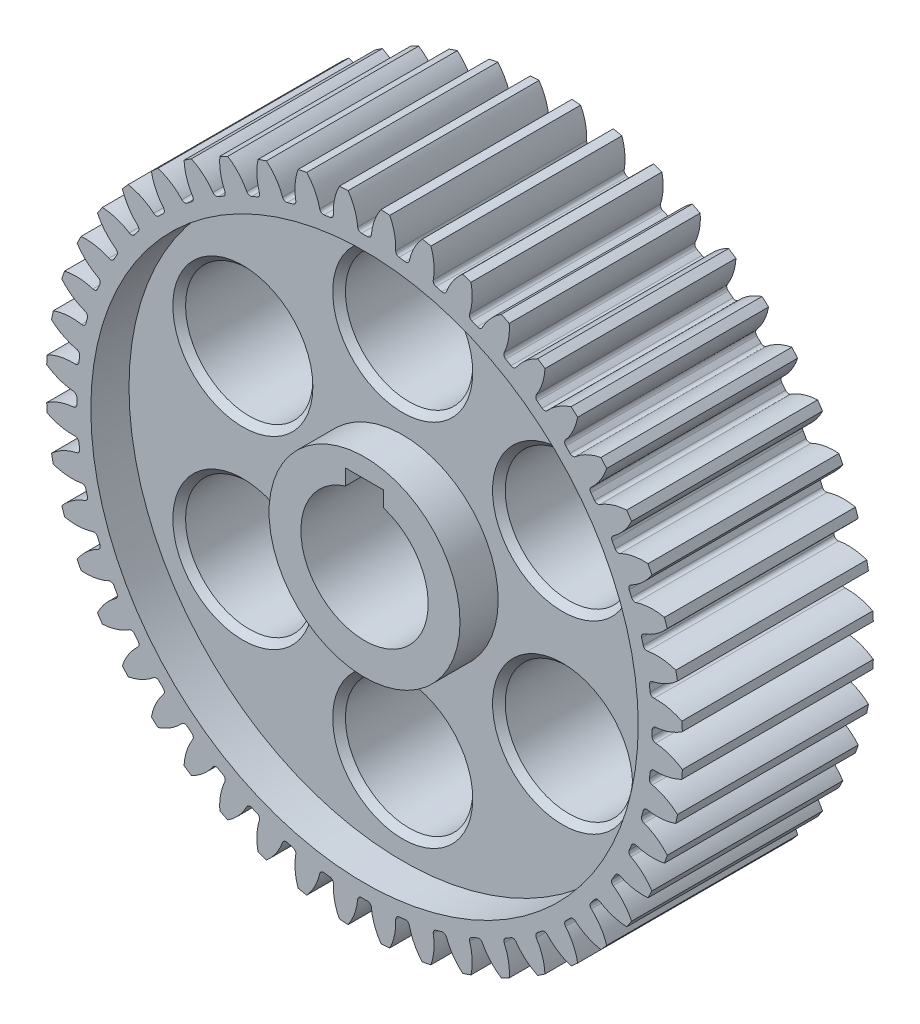
SolidWorks part; units mm, degrees
material "1023 Carbon Steel Sheet (SS)"
ref_plane "Front Plane" through (0, 0, 0) normal (0, 0, 1) x (1, 0, 0)
ref_plane "Top Plane" through (0, 0, 0) normal (0, 1, 0) x (1, 0, 0)
ref_plane "Right Plane" through (0, 0, 0) normal (1, 0, 0) x (0, 0, -1)
sketch "skBase" plane through (0, 0, 0) normal (0, 0, 1) x (1, 0, 0)
  circle A0 centre (0, 0) radius 24
  circle A1 centre (0, 0) radius 25
  circle A2 centre (0, 0) radius 22.6
  dimension "D1" = 48
  dimension "D2" = 1
  dimension "D3" = 2.4
extrude "Base" add sketch "skBase" along normal mid plane 15 contours A1
sketch "skToothProfile" plane through (0, 0, 0) normal (0, 0, 1) x (1, 0, 0)
  line L0 (0, 0) -> (0, 25) construction
  line L1 (-0.7853, 23.9872) -> (0.7853, 23.9872) construction
  line L2 (-0.5229, 22.5939) -> (0, 0) construction
  line L3 (0, 21.8297) -> (-1.5021, 25.9566) construction
  line L4 (0, 0) -> (1.6351, 24.9465) construction
  line L5 (0.7853, 23.9872) -> (2.3524, 23.8844) construction
  circle A0 centre (0, 0) radius 25 construction
  arc A1 (-0.5229, 22.5939) -> (-2.1677, 25.9095) centre (-4.8908, 22.4929) ccw
  arc A2 (0.5229, 22.5939) -> (2.1677, 25.9095) centre (4.8908, 22.4929) cw
  circle A3 centre (0, 0) radius 22.6 construction
  arc A4 (0.5229, 22.5939) -> (-0.5229, 22.5939) centre (0, 0) ccw
  circle A5 centre (0, 0) radius 24 construction
  circle A6 centre (0, 0) radius 25 construction
  circle A7 centre (0, 0) radius 26
  arc A8 (2.1677, 25.9095) -> (-2.1677, 25.9095) centre (0, 0) ccw
  dimension "D2" = 20
  dimension "D3" = 3.75
  dimension "D1" = 1
extrude "ToothProfile" cut sketch "skToothProfile" against normal through all and the other way through all
fillet "FilletToothProfile" radius 0.3 2 edges at (0.5229, 22.5939, 0) (-0.5229, 22.5939, 0)
pattern_circular "CirPatternTeeth" count 48 over 360 about axis through (0, 0, 0) along (0, 0, 1) of "ToothProfile", "FilletToothProfile"
sketch "skChaveta" plane through (0, 0, 7.5) normal (0, 0, 1) x (1, 0, 0)
  line L0 (0, 5) -> (0, 0) construction
  line L2 (-1.5, 6) -> (1.5, 6)
  line L3 (-1.5, 6) -> (-1.5, 3)
  line L4 (-1.5, 3) -> (1.5, 3)
  line L5 (1.5, 6) -> (1.5, 3)
  line L6 (-1.5, 6) -> (1.5, 3) construction
  line L7 (-1.5, 3) -> (1.5, 6) construction
  circle A0 centre (0, 0) radius 5
  point P4 (0, 4.5)
  dimension "D1" = 10
  dimension "D2" = 8
  dimension "D3" = 3
  dimension "D4" = 3
extrude "Chaveta" cut sketch "skChaveta" against normal through all contours L2 L5 L4 L3 | A0
sketch "skRebaixo" plane through (0, 0, 7.5) normal (0, 0, 1) x (1, 0, 0)
  circle A0 centre (0, 0) radius 21.5
  circle A1 centre (0, 0) radius 7.5
  dimension "D1" = 43
  dimension "D2" = 15
extrude "Rebaixo" cut sketch "skRebaixo" against normal blind 3
mirror "MirrorRebaixo" about plane through (0, 0, 0) normal (0, 0, 1) of "Rebaixo"
sketch "skBalanceamento" plane through (0, 0, -4.5) normal (0, 0, -1) x (-1, 0, 0)
  line L0 (0, 0) -> (0, 14.5) construction
  circle A0 centre (0, 14.5) radius 5
  dimension "D1" = 10
  dimension "D2" = 14.5
extrude "Balanceamento" cut sketch "skBalanceamento" against normal through all
chamfer "ChamferBalanceamento" distance 0.5 angle 45 2 edges at (-5, 14.5, -4.5) (5, 14.5, 4.5)
pattern_circular "CirPattern1" count 6 over 360 about axis through (0, 0, 0) along (0, 0, 1) of "Balanceamento", "ChamferBalanceamento"
equation "\"Module\"= 1mm"
equation "\"Number_Of_Teeth\"= 48"
equation "\"D1@skBase\"=\"Module\" * \"Number_Of_Teeth\""
equation "\"D2@skBase\"=\"Module\""
equation "\"D3@skBase\"=\"Module\" * if( \"Module\" >=1.25, 2.25, 2.4)"
equation "\"Pressure_Angle\"= 20deg"
equation "\"D2@skToothProfile\"=\"Pressure_Angle\""
equation "\"D3@skToothProfile\"=180 / \"Number_Of_Teeth\""
equation "\"D1@FilletToothProfile\"= 0.3 * \"Module\""
equation "\"D1@CirPatternTeeth\"=\"Number_Of_Teeth\""
equation "\"Width\"= 15mm"
equation "\"D1@Base\"=\"Width\""
